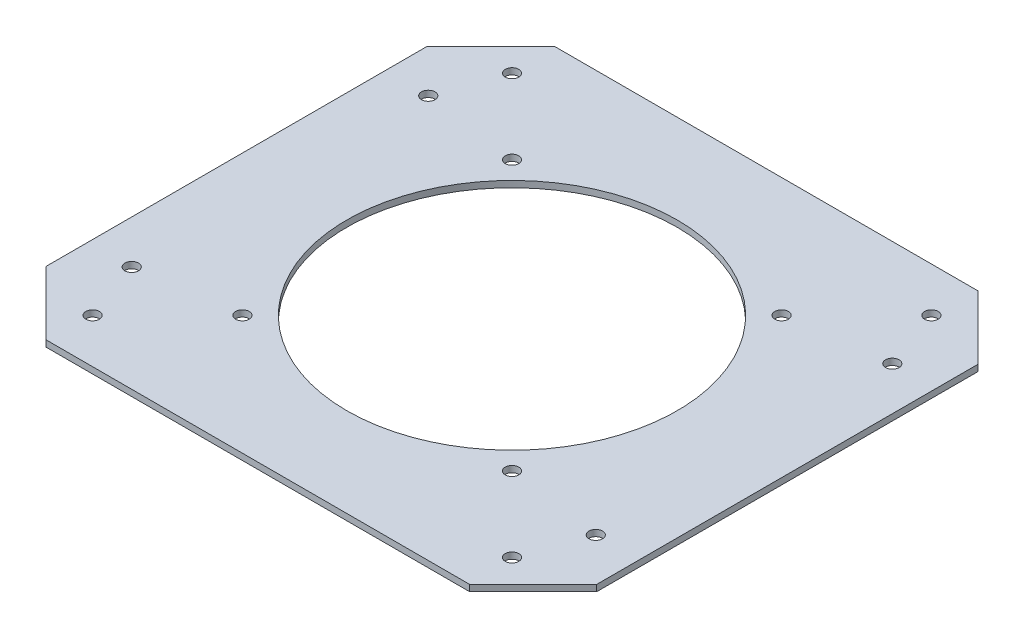
SolidWorks part; units mm, degrees
ref_plane "Front Plane" through (0, 0, 0) normal (0, 0, 1) x (1, 0, 0)
ref_plane "Top Plane" through (0, 0, 0) normal (0, 1, 0) x (1, 0, 0)
ref_plane "Right Plane" through (0, 0, 0) normal (1, 0, 0) x (0, 0, -1)
sketch "Sketch1" plane through (0, 0, 0) normal (0, 1, 0) x (1, 0, 0)
  line L1 (58.25, 0) -> (58.25, 39)
  line L3 (-58.5, 0) -> (-58.5, 39)
  line L4 (58.25, 0) -> (58.25, -39)
  line L5 (-58.5, 0) -> (-58.5, -39)
  line L8 (-39, -58.5) -> (-58.5, -39)
  line L10 (39, -58.5) -> (58.25, -39)
  line L12 (0, -85) -> (-39, -85)
  line L13 (-39, -85) -> (-39, -58.5)
  line L14 (0, -85) -> (39, -85)
  line L15 (39, -85) -> (39, -58.5)
  arc A0 (-58.5, 39) -> (58.25, 39) centre (-0.125, -19.9736) cw
  circle A1 centre (-54.75, -35.25) radius 1.6
  circle A2 centre (54.75, -35.25) radius 1.6
  circle A3 centre (54.75, 35.25) radius 1.6
  circle A4 centre (-54.75, 35.25) radius 1.6
  circle A5 centre (-35.5, -59.5) radius 1.6
  circle A6 centre (-35.5, -69.5) radius 1.6
  circle A7 centre (35.5, -69.5) radius 1.6
  circle A8 centre (35.5, -59.5) radius 1.6
extrude "Boss-Extrude1" add sketch "Sketch1" along normal blind 2
sketch "Sketch2" plane through (0, 2, 0) normal (0, 1, 0) x (1, 0, 0)
  line L0 (-39, -58.5) -> (39, -58.5)
  line L1 (39, -58.5) -> (39, -85)
  line L2 (39, -85) -> (-39, -85)
  line L3 (-39, -85) -> (-39, -58.5)
extrude "Cut-Extrude1" cut sketch "Sketch2" against normal blind 2
sketch "Sketch3" plane through (0, 2, 0) normal (0, 1, 0) x (1, 0, 0)
  line L0 (-39, -58.5) -> (39, -58.5)
  line L1 (39, -58.5) -> (39, -49.7913)
  line L2 (39, -49.7913) -> (-39, -49.7913)
  line L3 (-39, -49.7913) -> (-39, -58.5)
extrude "Boss-Extrude2" add sketch "Sketch3" against normal blind 2
sketch "Sketch4" plane through (0, 2, 0) normal (0, 1, 0) x (1, 0, 0)
  circle A0 centre (54, 8) radius 1.6
  circle A1 centre (54, -7.0054) radius 1.6
  circle A2 centre (-54, -7.0054) radius 1.6
  circle A3 centre (-54, 8) radius 1.6
extrude "Cut-Extrude2" cut sketch "Sketch4" against normal blind 2
sketch "Sketch5" plane through (0, 2, 0) normal (0, 1, 0) x (1, 0, 0)
  circle A0 centre (-8, 44) radius 1.6
  circle A1 centre (8, 44) radius 1.6
extrude "Cut-Extrude4" cut sketch "Sketch5" against normal blind 2
sketch "Sketch6" plane through (0, 2, 0) normal (0, 1, 0) x (1, 0, 0)
  line L0 (0, 53.9968) -> (0, 54)
  arc A0 (-58.5, 39) -> (58.25, 39) centre (-0.125, -67.1136) cw
  arc A1 (-58.5, 39) -> (58.25, 39) centre (-0.125, 11.9782) cw
extrude "Cut-Extrude5" cut sketch "Sketch6" against normal blind 2
sketch "Sketch7" plane through (0, 2, 0) normal (0, 1, 0) x (1, 0, 0)
  line L1 (26, 0) -> (26, 16)
  line L2 (26, 16) -> (23, 16)
  line L3 (26, 0) -> (26, -16)
  line L4 (26, -16) -> (23, -16)
  line L5 (23, -16) -> (23, 16)
  line L7 (-23, -16) -> (-23, 16)
  line L8 (-26, -16) -> (-23, -16)
  line L9 (-26, 0) -> (-26, -16)
  line L10 (-26, 16) -> (-23, 16)
  line L11 (-26, 0) -> (-26, 16)
extrude "Boss-Extrude3" add sketch "Sketch7" along normal blind 10
sketch "Sketch8" plane through (0, 12, 0) normal (0, 1, 0) x (1, 0, 0)
  line L0 (37, 27) -> (37, -44)
  line L1 (0, 27) -> (27, 27)
  line L2 (0, 27) -> (-27, 27)
  line L3 (27, 30) -> (27, 27)
  line L4 (0, -44) -> (-37, -44)
  line L5 (-37, -44) -> (-37, 27)
  line L6 (0, -44) -> (37, -44)
  line L7 (33, 30) -> (33, 27)
  line L8 (33, 27) -> (37, 27)
  line L10 (-33, 30) -> (-33, 27)
  line L11 (-27, 30) -> (-27, 27)
  line L12 (-33, 27) -> (-37, 27)
  circle A0 centre (33, -40) radius 1.6
  circle A1 centre (30, 30) radius 1.6
  arc A2 (33, 30) -> (27, 30) centre (30, 30) ccw
  circle A3 centre (-33, -40) radius 1.6
  circle A4 centre (-30, 30) radius 1.6
  arc A5 (-33, 30) -> (-27, 30) centre (-30, 30) cw
extrude "Boss-Extrude4" add sketch "Sketch8" along normal blind 1.5
sketch "Sketch9" plane through (0, 13.5, 0) normal (0, 1, 0) x (1, 0, 0)
  line L1 (45, 42) -> (-45, 42)
  line L2 (-45, 42) -> (-45, -48.1466)
  line L3 (-45, -48.1466) -> (45, -48.1466)
  line L4 (45, 42) -> (45, -48.1466)
  circle A0 centre (-30, 30) radius 1.6
  circle A1 centre (30, 30) radius 1.6
  circle A2 centre (33, -40) radius 1.6
  circle A3 centre (-33, -40) radius 1.6
  point P8 (0, -48.1466)
extrude "Boss-Extrude5" add sketch "Sketch9" against normal blind 1.5
sketch "Sketch10" plane through (0, 13.5, 0) normal (0, 1, 0) x (1, 0, 0)
  line L0 (33, -21.5) -> (33, -36)
  line L1 (27.5, -16) -> (33, -21.5)
  line L2 (-33.0003, 26.9997) -> (-27.5, 21.4995)
  line L3 (-27.5, 21.4995) -> (-27.5, 0)
  line L4 (-45, 42) -> (45, 42)
  line L5 (27.5, 0) -> (27.5, -16)
  line L6 (-26.9997, 33.0003) -> (-17.2495, 23.25)
  line L7 (-17.2495, 23.25) -> (17.2495, 23.25)
  line L8 (-27.5, 0) -> (-27.5, -16)
  line L9 (45, 42) -> (45, -48.1466)
  line L10 (26.9997, 33.0003) -> (17.2495, 23.25)
  line L11 (-27.5, -16) -> (-33, -21.5)
  line L12 (-33, -21.5) -> (-33, -36)
  line L13 (-45, -48.1466) -> (45, -48.1466) construction
  line L14 (33, -44) -> (-33, -44)
  line L15 (27.5, 21.4995) -> (27.5, 0)
  line L16 (33.0003, 26.9997) -> (27.5, 21.4995)
  line L17 (45, -48.1466) -> (45, 42) construction
  line L18 (45, -48.1466) -> (-45, -48.1466)
  line L19 (-45, 42) -> (-45, -48.1466) construction
  line L20 (-45, -48.1466) -> (-45, 42)
  arc A0 (-26.9997, 33.0003) -> (-33.0003, 26.9997) centre (-30, 30) ccw
  arc A1 (-33, -36) -> (-33, -44) centre (-33, -40) ccw
  arc A5 (33, -36) -> (33, -44) centre (33, -40) cw
  arc A6 (26.9997, 33.0003) -> (33.0003, 26.9997) centre (30, 30) cw
extrude "Cut-Extrude6" cut sketch "Sketch10" against normal blind 1.5
sketch "Sketch11" plane through (0, 13.5, 0) normal (0, 1, 0) x (1, 0, 0)
  line L0 (-27.5, -16) -> (-27.5, -36)
  line L1 (-33, -36) -> (-27.5, -36)
  line L2 (-27.5, -16) -> (-33, -16)
  line L3 (-33, -16) -> (-33, -36)
  line L5 (33, -16) -> (33, -36)
  line L6 (27.5, -16) -> (33, -16)
  line L7 (33, -36) -> (27.5, -36)
  line L8 (27.5, -16) -> (27.5, -36)
extrude "Cut-Extrude7" cut sketch "Sketch11" against normal blind 10
sketch "Sketch13" plane through (0, 2, 0) normal (0, 1, 0) x (1, 0, 0)
  circle A0 centre (-54, -7.1181) radius 1.6
  circle A1 centre (-54, 8) radius 1.6
  circle A2 centre (54, 8) radius 1.6
  circle A3 centre (54, -7.1181) radius 1.6
extrude "Cut-Extrude8" cut sketch "Sketch13" against normal blind 10
sketch "Sketch14" plane through (0, 2, 0) normal (0, 1, 0) x (1, 0, 0)
  circle A0 centre (0, 0) radius 95.5604
extrude "Cut-Extrude9" cut sketch "Sketch14" along normal blind 57
sketch "Sketch15" plane through (0, 2, 0) normal (0, 1, 0) x (1, 0, 0)
  line L5 (-57.5784, 32.4216) -> (-36.5065, 11.3496)
  line L7 (-51.9216, 38.0784) -> (-33.0532, 19.21)
  line L10 (57.5784, 32.4216) -> (36.5065, 11.3496)
  line L11 (51.9216, 38.0784) -> (33.0532, 19.21)
  line L12 (57.5784, -32.4216) -> (36.5065, -11.3496)
  line L13 (51.9216, -38.0784) -> (33.0532, -19.21)
  line L14 (-51.9216, -38.0784) -> (-33.0532, -19.21)
  line L15 (-57.5784, -32.4216) -> (-36.5065, -11.3496)
  circle A0 centre (54.75, 35.25) radius 1.6
  circle A1 centre (-54.75, 35.25) radius 1.6
  circle A2 centre (-54.75, -35.25) radius 1.6
  circle A3 centre (54.75, -35.25) radius 1.6
  arc A4 (-33.0532, -19.21) -> (33.0532, -19.21) centre (0, 0) ccw
  arc A5 (-51.9216, 38.0784) -> (-57.5784, 32.4216) centre (-54.75, 35.25) ccw
  arc A6 (51.9216, 38.0784) -> (57.5784, 32.4216) centre (54.75, 35.25) cw
  arc A7 (51.9216, -38.0784) -> (57.5784, -32.4216) centre (54.75, -35.25) ccw
  arc A8 (-51.9216, -38.0784) -> (-57.5784, -32.4216) centre (-54.75, -35.25) cw
  arc A9 (36.5065, -11.3496) -> (36.5065, 11.3496) centre (0, 0) ccw
  arc A10 (-36.5065, 11.3496) -> (-36.5065, -11.3496) centre (0, 0) ccw
  arc A11 (33.0532, 19.21) -> (-33.0532, 19.21) centre (0, 0) ccw
  circle A12 centre (-44, 24.5) radius 1.6
  circle A13 centre (44, 24.5) radius 1.6
  circle A14 centre (44, -24.5) radius 1.6
  circle A15 centre (-44, -24.5) radius 1.6
extrude "Boss-Extrude6" add sketch "Sketch15" along normal blind 2
sketch "Sketch16" plane through (0, 0, 0) normal (0, -1, 0) x (-1, 0, 0)
  circle A0 centre (0, 0) radius 99.5218
extrude "Cut-Extrude10" cut sketch "Sketch16" against normal blind 2
sketch "Sketch17" plane through (0, 4, 0) normal (0, 1, 0) x (1, 0, 0)
  circle A1 centre (20.8597, 20.8597) radius 1.6
  circle A2 centre (-20.8597, 20.8597) radius 1.6
  circle A3 centre (-20.8597, -20.8597) radius 1.6
  circle A4 centre (20.8597, -20.8597) radius 1.6
extrude "Cut-Extrude11" cut sketch "Sketch17" against normal blind 2
sketch "Sketch18" plane through (0, 4, 0) normal (0, 1, 0) x (1, 0, 0)
  line L0 (-33.0532, 19.21) -> (-28.3676, 14.5245)
  line L1 (-36.5065, 11.3496) -> (-29.2118, 4.055)
  line L2 (0, 0) -> (0, 7.7023)
  line L3 (0, 0) -> (8.2422, 0)
  line L4 (-36.5065, -11.3496) -> (-29.2118, -4.055)
  line L5 (-33.0532, -19.21) -> (-28.3676, -14.5245)
  line L6 (33.0532, -19.21) -> (28.3676, -14.5245)
  line L7 (36.5065, -11.3496) -> (29.2118, -4.055)
  line L8 (36.5065, 11.3496) -> (29.2118, 4.055)
  line L9 (33.0532, 19.21) -> (28.3676, 14.5245)
  line L10 (-36.5065, 11.3496) -> (-63.8945, -1.7518)
  line L11 (-63.8945, -1.7518) -> (-36.5065, -11.3496)
  line L12 (-33.0532, -19.21) -> (-26.4511, -51.8879)
  line L13 (-26.4511, -51.8879) -> (29.2118, -51.0417)
  line L14 (29.2118, -51.0417) -> (33.0532, -19.21)
  line L15 (36.5065, -11.3496) -> (60.1763, -3.2326)
  line L16 (60.1763, -3.2326) -> (36.5065, 11.3496)
  line L17 (33.0532, 19.21) -> (27.6286, 53.1093)
  line L18 (27.6286, 53.1093) -> (-39.0288, 61.1533)
  line L19 (-39.0288, 61.1533) -> (-33.0532, 19.21)
  circle A0 centre (0, 0) radius 26
  circle A1 centre (0, 0) radius 33
extrude "Cut-Extrude12" cut sketch "Sketch18" against normal blind 2
sketch "Sketch19" plane through (0, 4, 0) normal (0, 1, 0) x (1, 0, 0)
  line L5 (-3, 3) -> (-3, 25.8263)
  line L6 (3, 3) -> (3, 25.8263)
  line L7 (3, -3) -> (3, -25.8263)
  line L8 (-3, -3) -> (-3, -25.8263)
  line L9 (25.8263, -3) -> (3, -3)
  line L10 (25.8263, 3) -> (3, 3)
  line L11 (-3, 3) -> (-25.8263, 3)
  line L12 (-3, -3) -> (-25.8263, -3)
  circle A0 centre (0, 0) radius 26 construction
  arc A1 (-25.8263, 3) -> (-25.8263, -3) centre (0, 0) ccw
  arc A2 (3, 25.8263) -> (-3, 25.8263) centre (0, 0) ccw
  arc A3 (25.8263, -3) -> (25.8263, 3) centre (0, 0) ccw
  arc A4 (-3, -25.8263) -> (3, -25.8263) centre (0, 0) ccw
extrude "Boss-Extrude7" add sketch "Sketch19" against normal up to surface (2 mm away)
sketch "Sketch20" plane through (0, 4, 0) normal (0, 1, 0) x (1, 0, 0)
  line L0 (48, -24.5) -> (48, 24.5)
  line L1 (40, 24.5) -> (40, -24.5)
  line L3 (-40, 24.5) -> (-40, -24.5)
  line L4 (-48, -24.5) -> (-48, 24.5)
  arc A0 (48, 24.5) -> (40, 24.5) centre (44, 24.5) ccw
  arc A1 (40, -24.5) -> (48, -24.5) centre (44, -24.5) ccw
  circle A2 centre (44, -24.5) radius 1.6
  circle A3 centre (44, 24.5) radius 1.6
  arc A4 (-40, -24.5) -> (-48, -24.5) centre (-44, -24.5) cw
  circle A5 centre (-44, 24.5) radius 1.6
  circle A6 centre (-44, -24.5) radius 1.6
  arc A7 (-48, 24.5) -> (-40, 24.5) centre (-44, 24.5) cw
extrude "Boss-Extrude8" add sketch "Sketch20" against normal up to surface (2 mm away)
sketch "Sketch21" plane through (0, 4, 0) normal (0, 1, 0) x (1, 0, 0)
  circle A0 centre (0, 0) radius 33
  circle A1 centre (0, 0) radius 90.9891
extrude "Cut-Extrude13" cut sketch "Sketch21" against normal blind 10
sketch "Sketch22" plane through (0, 4, 0) normal (0, 1, 0) x (1, 0, 0)
  line L2 (-51.9438, 37.8284) -> (-29.2993, 15.1839)
  line L4 (-57.6007, 32.1716) -> (-29.3793, 3.9502)
  line L5 (-29.3793, 3.9502) -> (-29.2993, 15.1839)
  line L6 (29.3793, 3.9502) -> (29.2993, 15.1839)
  line L7 (57.6007, 32.1716) -> (29.3793, 3.9502)
  line L8 (51.9438, 37.8284) -> (29.2993, 15.1839)
  line L10 (51.9438, -37.8284) -> (29.2993, -15.1839)
  line L11 (57.6007, -32.1716) -> (29.3793, -3.9502)
  line L12 (29.3793, -3.9502) -> (29.2993, -15.1839)
  line L13 (-29.3793, -3.9502) -> (-29.2993, -15.1839)
  line L14 (-57.6007, -32.1716) -> (-29.3793, -3.9502)
  line L15 (-51.9438, -37.8284) -> (-29.2993, -15.1839)
  arc A0 (-51.9438, 37.8284) -> (-57.6007, 32.1716) centre (-54.7723, 35) ccw
  circle A1 centre (-54.7723, 35) radius 1.6
  circle A2 centre (0, 0) radius 33 construction
  circle A3 centre (54.7723, 35) radius 1.6
  arc A4 (51.9438, 37.8284) -> (57.6007, 32.1716) centre (54.7723, 35) cw
  arc A5 (51.9438, -37.8284) -> (57.6007, -32.1716) centre (54.7723, -35) ccw
  circle A6 centre (54.7723, -35) radius 1.6
  circle A7 centre (-54.7723, -35) radius 1.6
  arc A8 (-51.9438, -37.8284) -> (-57.6007, -32.1716) centre (-54.7723, -35) cw
extrude "Boss-Extrude9" add sketch "Sketch22" against normal up to surface (2 mm away)
sketch "Sketch23" plane through (0, 4, 0) normal (0, 1, 0) x (1, 0, 0)
  line L0 (-65, 45) -> (-54.3934, 55.6066)
  line L2 (60, 0) -> (60, 45)
  line L4 (-65, 0) -> (-65, 45)
  line L5 (-65, 0) -> (-65, -45)
  line L7 (60, -45) -> (60, 0)
  line L9 (60, 45) -> (49.3934, 55.6066)
  line L10 (49.3934, 55.6066) -> (-54.3934, 55.6066)
  line L11 (-65, -45) -> (-54.3934, -55.6066)
  line L12 (60, -45) -> (49.3934, -55.6066)
  line L13 (-54.3934, -55.6066) -> (49.3934, -55.6066)
  circle A0 centre (54.7723, 35) radius 1.6
  circle A1 centre (54.7723, -35) radius 1.6
  circle A2 centre (-54.7723, -35) radius 1.6
  circle A3 centre (-54.7723, 35) radius 1.6
  circle A4 centre (0, 0) radius 38
extrude "Boss-Extrude10" add sketch "Sketch23" along normal blind 1.5
sketch "Sketch24" plane through (0, 4, 0) normal (0, -1, 0) x (-1, 0, 0)
  circle A0 centre (0, 0) radius 98.5883
extrude "Cut-Extrude14" cut sketch "Sketch24" along normal blind 27.5
sketch "Sketch25" plane through (0, 5.5, 0) normal (0, 1, 0) x (1, 0, 0)
  circle A0 centre (0, 0) radius 39
extrude "Cut-Extrude15" cut sketch "Sketch25" against normal blind 27.5
sketch "Sketch27" plane through (0, 5.5, 0) normal (0, 1, 0) x (1, 0, 0)
  circle A0 centre (31.8198, 31.8198) radius 1.6
  circle A1 centre (-31.8198, 31.8198) radius 1.6
  circle A2 centre (31.8198, -31.8198) radius 1.6
  circle A3 centre (-31.8198, -31.8198) radius 1.6
extrude "Cut-Extrude16" cut sketch "Sketch27" against normal blind 27.5
sketch "Sketch29" plane through (0, 5.5, 0) normal (0, 1, 0) x (1, 0, 0)
  line L1 (65, -45) -> (65, 45)
  line L3 (65, 45) -> (50, 60)
  line L4 (50, 60) -> (-50, 60)
  line L5 (-65, 45) -> (-50, 60)
  line L6 (-65, -45) -> (-65, 45)
  line L7 (-65, -45) -> (-50, -60)
  line L8 (50, -60) -> (-50, -60)
  line L9 (65, -45) -> (50, -60)
  circle A0 centre (-31.8198, 31.8198) radius 1.6
  circle A1 centre (31.8198, 31.8198) radius 1.6
  circle A2 centre (54.7723, 35) radius 1.6
  circle A3 centre (-54.7723, 35) radius 1.6
  circle A4 centre (-54.7723, -35) radius 1.6
  circle A5 centre (-31.8198, -31.8198) radius 1.6
  circle A6 centre (31.8198, -31.8198) radius 1.6
  circle A7 centre (54.7723, -35) radius 1.6
  circle A8 centre (0, 0) radius 39
  point P15 (0, 0)
extrude "Boss-Extrude14" add sketch "Sketch29" against normal blind 1.5
sketch "Sketch30" plane through (0, 5.5, 0) normal (0, 1, 0) x (1, 0, 0)
  circle A0 centre (49.4975, -49.4975) radius 1.6
  circle A1 centre (-49.4975, -49.4975) radius 1.6
  circle A2 centre (-49.4975, 49.4975) radius 1.6
  circle A3 centre (49.4975, 49.4975) radius 1.6
  point P12 (0, 0)
  dimension "D1" = 4
extrude "Cut-Extrude17" cut sketch "Sketch30" against normal blind 10
